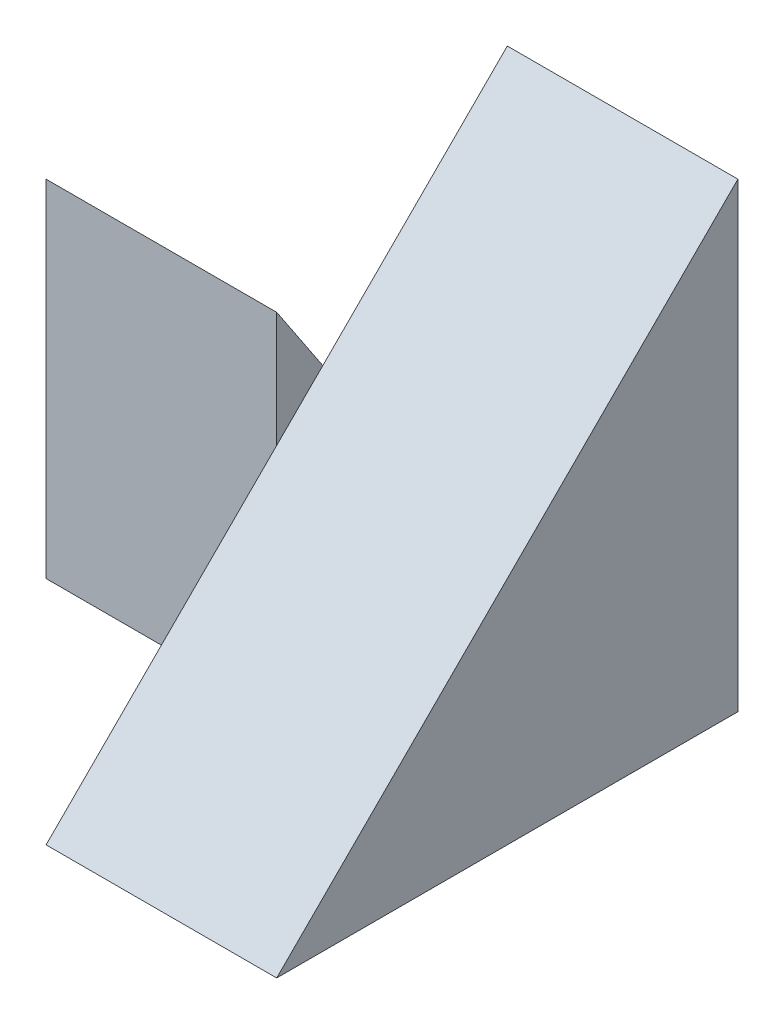
SolidWorks part; units mm, degrees
ref_plane "Front Plane" through (0, 0, 0) normal (0, 0, 1) x (1, 0, 0)
ref_plane "Top Plane" through (0, 0, 0) normal (0, 1, 0) x (1, 0, 0)
ref_plane "Right Plane" through (0, 0, 0) normal (1, 0, 0) x (0, 0, -1)
sketch "Sketch1" plane through (0, 0, 0) normal (1, 0, 0) x (0, 0, -1)
  line L1 (0, 0) -> (4, 0)
  line L2 (0, 0) -> (0, 4)
  line L3 (0, 4) -> (4, 4)
  line L4 (4, 0) -> (4, 4)
  dimension "D1" = 4
  dimension "D2" = 4
extrude "Boss-Extrude1" add sketch "Sketch1" along normal blind 2
sketch "Sketch2" plane through (0, 0, 0) normal (-1, 0, 0) x (0, 0, 1)
  line L1 (-4, 0) -> (-2, 0)
  line L2 (-4, 0) -> (-4, 3)
  line L3 (-4, 3) -> (-2, 3)
  line L4 (-2, 0) -> (-2, 3)
  dimension "D1" = 3
  dimension "D2" = 2
extrude "Boss-Extrude2" add sketch "Sketch2" along normal blind 2
sketch "Sketch3" plane through (-2, 0, 0) normal (-1, 0, 0) x (0, 0, 1)
  line L0 (-2, 3) -> (-4, 0)
  line L1 (-4, 0) -> (-4, 3)
  line L2 (-4, 3) -> (-2, 3)
extrude "Cut-Extrude1" cut sketch "Sketch3" against normal blind 2
sketch "Sketch4" plane through (2, 0, 0) normal (1, 0, 0) x (0, 0, -1)
  line L0 (4, 4) -> (0, 0)
  line L1 (0, 0) -> (0, 4)
  line L2 (0, 4) -> (4, 4)
extrude "Cut-Extrude2" cut sketch "Sketch4" against normal blind 2
